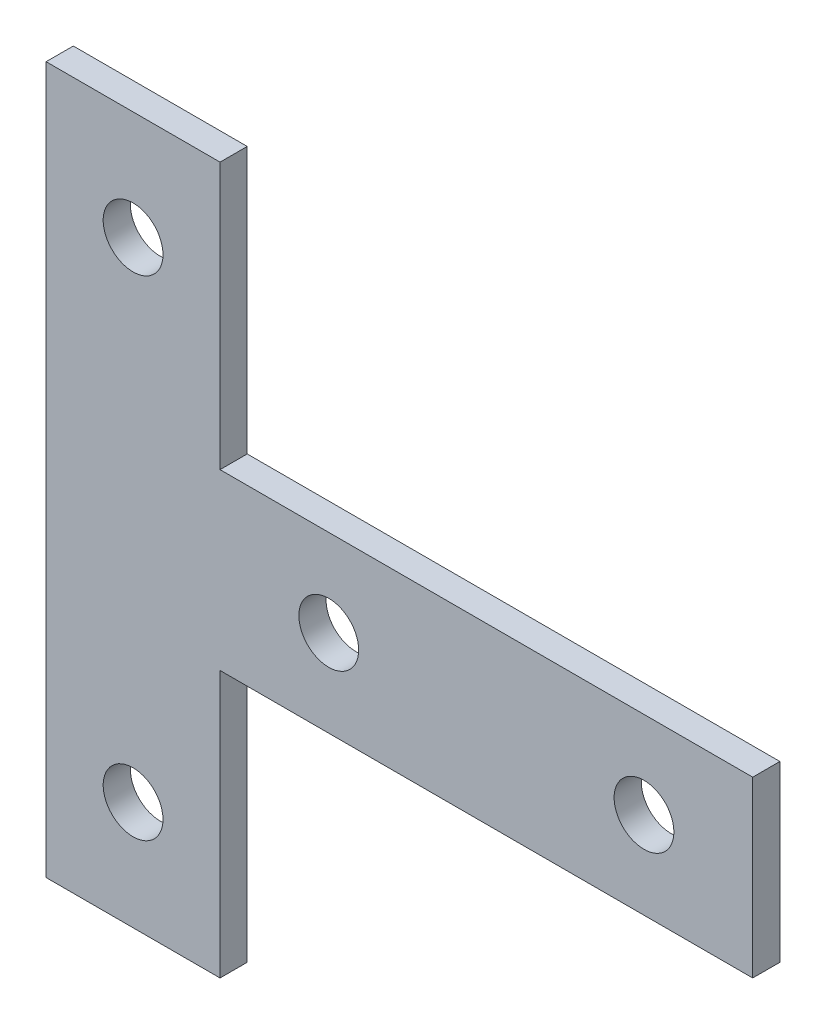
SolidWorks part; units mm, degrees
material "1023 碳钢板 (SS)"
ref_plane "前视基准面" through (0, 0, 0) normal (0, 0, 1) x (1, 0, 0)
ref_plane "上视基准面" through (0, 0, 0) normal (0, 1, 0) x (1, 0, 0)
ref_plane "右视基准面" through (0, 0, 0) normal (1, 0, 0) x (0, 0, -1)
sketch "草图1" plane through (0, 0, 0) normal (0, 0, 1) x (1, 0, 0)
  line L0 (-22.3167, 55.0308) -> (-22.3167, -9.9692)
  line L1 (-22.3167, -9.9692) -> (-6.3167, -9.9692)
  line L2 (-6.3167, -9.9692) -> (-6.3167, 14.5308)
  line L3 (-6.3167, 14.5308) -> (42.6833, 14.5308)
  line L4 (42.6833, 14.5308) -> (42.6833, 30.5308)
  line L5 (42.6833, 30.5308) -> (-6.3167, 30.5308)
  line L6 (-6.3167, 30.5308) -> (-6.3167, 55.0308)
  line L7 (-6.3167, 55.0308) -> (-22.3167, 55.0308)
  circle A2 centre (32.6833, 22.5308) radius 2.75
  circle A3 centre (3.6833, 22.5308) radius 2.75
  circle A4 centre (-14.3167, 0.0308) radius 2.75
  circle A5 centre (-14.3167, 45.0308) radius 2.75
extrude "凸台-拉伸1" add sketch "草图1" along normal blind 2.5
